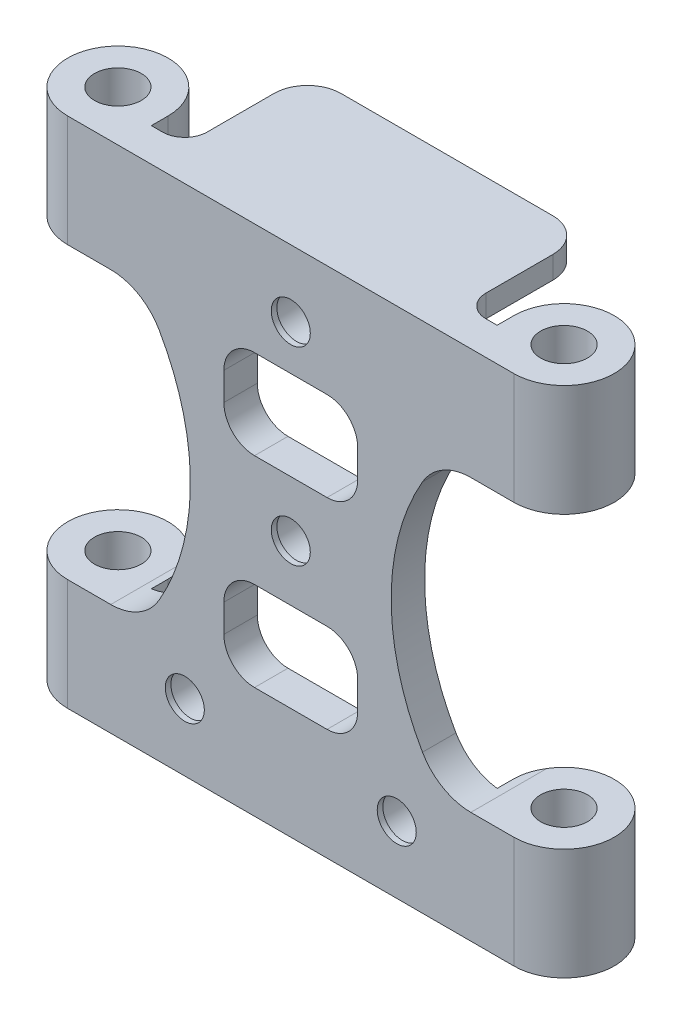
SolidWorks part; units mm, degrees
ref_plane "Front Plane" through (0, 0, 0) normal (0, 0, 1) x (1, 0, 0)
ref_plane "Top Plane" through (0, 0, 0) normal (0, 1, 0) x (1, 0, 0)
ref_plane "Right Plane" through (0, 0, 0) normal (1, 0, 0) x (0, 0, -1)
sketch "Sketch1" plane through (0, 0, 0) normal (0, 0, 1) x (1, 0, 0)
  line L0 (-17, 23) -> (17, -23) construction
  line L1 (-17, 23) -> (17, 23)
  line L2 (-17, 23) -> (-17, 13)
  line L3 (-17, -23) -> (17, -23)
  line L4 (17, 23) -> (17, 13)
  line L5 (0, 0) -> (0, 26.1672) construction
  line L6 (-3.25, 13) -> (3.25, 13)
  line L7 (-6, 10.25) -> (-6, 7.75)
  line L8 (-3.25, 5) -> (3.25, 5)
  line L9 (6, 10.25) -> (6, 7.75)
  line L10 (-3.25, -5) -> (3.25, -5)
  line L11 (-6, -7.75) -> (-6, -10.25)
  line L12 (-3.25, -13) -> (3.25, -13)
  line L13 (6, -7.75) -> (6, -10.25)
  line L14 (-17, 13) -> (-13.5, 13)
  line L16 (-13.5, -13) -> (-17, -13)
  line L17 (17, 13) -> (13.5, 13)
  line L19 (13.5, -13) -> (17, -13)
  line L20 (-17, -13) -> (-17, -23)
  line L21 (17, -13) -> (17, -23)
  arc A0 (3.25, -13) -> (6, -10.25) centre (3.25, -10.25) ccw
  arc A1 (3.25, -5) -> (6, -7.75) centre (3.25, -7.75) cw
  arc A2 (-6, -10.25) -> (-3.25, -13) centre (-3.25, -10.25) ccw
  arc A3 (-3.25, -5) -> (-6, -7.75) centre (-3.25, -7.75) ccw
  arc A4 (3.25, 5) -> (6, 7.75) centre (3.25, 7.75) ccw
  arc A5 (3.25, 13) -> (6, 10.25) centre (3.25, 10.25) cw
  arc A6 (-6, 7.75) -> (-3.25, 5) centre (-3.25, 7.75) ccw
  arc A7 (-3.25, 13) -> (-6, 10.25) centre (-3.25, 10.25) ccw
  circle A8 centre (0, 0) radius 1.75
  circle A9 centre (0, 17) radius 1.75
  circle A11 centre (-9.5, -17) radius 1.75
  circle A12 centre (9.5, -17) radius 1.75
  arc A13 (-13.5, 13) -> (-13.5, -13) centre (-30.0278, 0) cw
  arc A14 (13.5, 13) -> (13.5, -13) centre (30.0278, 0) ccw
  point P4 (0, 0)
  point P26 (6, 5)
  point P29 (6, 13)
  point P34 (-6, 13)
  point P54 (-9, 0)
  point P55 (9, 0)
  dimension "D7" = 2.75
  dimension "D14" = 3.5
  dimension "D15" = 17
  dimension "D18" = 3.5
  dimension "D1" = 34
  dimension "D2" = 46
  dimension "D3" = 12
  dimension "D4" = 8
  dimension "D5" = 10
  dimension "D6" = 10
  dimension "D8" = 2.5
  dimension "D9" = 10
  dimension "D10" = 10
  dimension "D11" = 18
  dimension "D12" = 23
  dimension "D13" = 23
  dimension "D16" = 17
  dimension "D17" = 19
extrude "Boss-Extrude1" add sketch "Sketch1" along normal blind 3
sketch "Sketch2" plane through (0, 23, 0) normal (0, 1, 0) x (1, 0, 0)
  line L0 (0, 0) -> (0, 10.8522) construction
  line L1 (17, 0) -> (-17, 0) construction
  line L2 (17, -3) -> (-17, -3) construction
  line L3 (-20, -3) -> (-15.5, -3)
  line L4 (-15.5, -3) -> (-15.5, 1.5)
  line L5 (20, -3) -> (15.5, -3)
  line L6 (15.5, -3) -> (15.5, 1.5)
  arc A0 (-15.5, 1.5) -> (-20, -3) centre (-20, 1.5) ccw
  circle A1 centre (-20, 1.5) radius 2.1
  arc A2 (20, -3) -> (15.5, 1.5) centre (20, 1.5) ccw
  circle A3 centre (20, 1.5) radius 2.1
  dimension "D1" = 9
  dimension "D2" = 4.2
  dimension "D5" = 4.5
  dimension "D6" = 40
extrude "Boss-Extrude2" add sketch "Sketch2" against normal blind 10
sketch "Sketch3" plane through (0, -23, 0) normal (0, -1, 0) x (1, 0, 0)
  line L2 (-15.5, 3) -> (-20, 3)
  line L3 (-15.5, -1.5) -> (-15.5, 3)
  line L4 (-15.5, 3) -> (-20, 3)
  line L5 (-15.5, -1.5) -> (-15.5, 3)
  line L6 (15.5, 3) -> (15.5, -1.5)
  line L7 (20, 3) -> (15.5, 3)
  line L8 (15.5, 3) -> (15.5, -1.5)
  line L9 (20, 3) -> (15.5, 3)
  circle A1 centre (20, -1.5) radius 2.1
  circle A2 centre (20, -1.5) radius 2.1
  circle A3 centre (-20, -1.5) radius 2.1
  circle A4 centre (-20, -1.5) radius 2.1
  arc A5 (-20, 3) -> (-15.5, -1.5) centre (-20, -1.5) ccw
  arc A6 (-20, 3) -> (-15.5, -1.5) centre (-20, -1.5) ccw
  arc A7 (15.5, -1.5) -> (20, 3) centre (20, -1.5) ccw
  arc A8 (15.5, -1.5) -> (20, 3) centre (20, -1.5) ccw
  dimension "D1" = 0
  dimension "D2" = 0
  dimension "D3" = 0
  dimension "D4" = 0
extrude "Boss-Extrude3" add sketch "Sketch3" against normal blind 10
sketch "Sketch4" plane through (0, 23, 0) normal (0, 1, 0) x (1, 0, 0)
  line L0 (15.5, 0) -> (-15.5, 0) construction
  line L1 (-12.5, 0) -> (12.5, 0)
  line L2 (-12.5, 0) -> (-12.5, 8)
  line L3 (-9.5, 11) -> (9.5, 11)
  line L4 (12.5, 0) -> (12.5, 8)
  line L5 (0, 0) -> (0, 15.7272) construction
  arc A0 (9.5, 11) -> (12.5, 8) centre (9.5, 8) cw
  arc A1 (-12.5, 8) -> (-9.5, 11) centre (-9.5, 8) cw
  point P11 (12.5, 11)
  point P14 (-12.5, 11)
  dimension "D3" = 3
  dimension "D1" = 25
  dimension "D2" = 11
extrude "Boss-Extrude4" add sketch "Sketch4" against normal blind 2
sketch "Sketch5" plane through (0, 0, 3) normal (0, 0, 1) x (1, 0, 0)
  line L1 (0, 5) -> (0, -5) construction
  line L2 (-3.25, 5) -> (3.25, 5) construction
  line L3 (3.25, -5) -> (-3.25, -5) construction
  circle A0 centre (0, 0) radius 3
  circle A1 centre (-9, 0) radius 2.25
  circle A2 centre (7.5, 0) radius 2.25
  point P6 (0, 0)
  dimension "D1" = 6
  dimension "D2" = 4.5
  dimension "D3" = 4.5
  dimension "D4" = 9
  dimension "D5" = 7.5
fillet "Fillet1" radius 2 3 edges at (-12.5, 22, 0) (12.5, 22, 0) (0, 21, 0)
sketch "Sketch6" plane through (0, 0, 0) normal (0, 0, -1) x (-1, 0, 0)
  circle A0 centre (0, 0) radius 2.1
  circle A2 centre (0, 17) radius 2.1
  circle A3 centre (-9.5, -17) radius 2.1
  circle A4 centre (9.5, -17) radius 2.1
  dimension "D1" = 4.2
extrude "Cut-Extrude1" cut sketch "Sketch6" against normal blind 2.5 and the other way through all
fillet "Fillet2" radius 5 4 edges at (-13.5, -13, 1.5) (13.5, -13, 1.5) (-13.5, 13, 1.5) (13.5, 13, 1.5)
